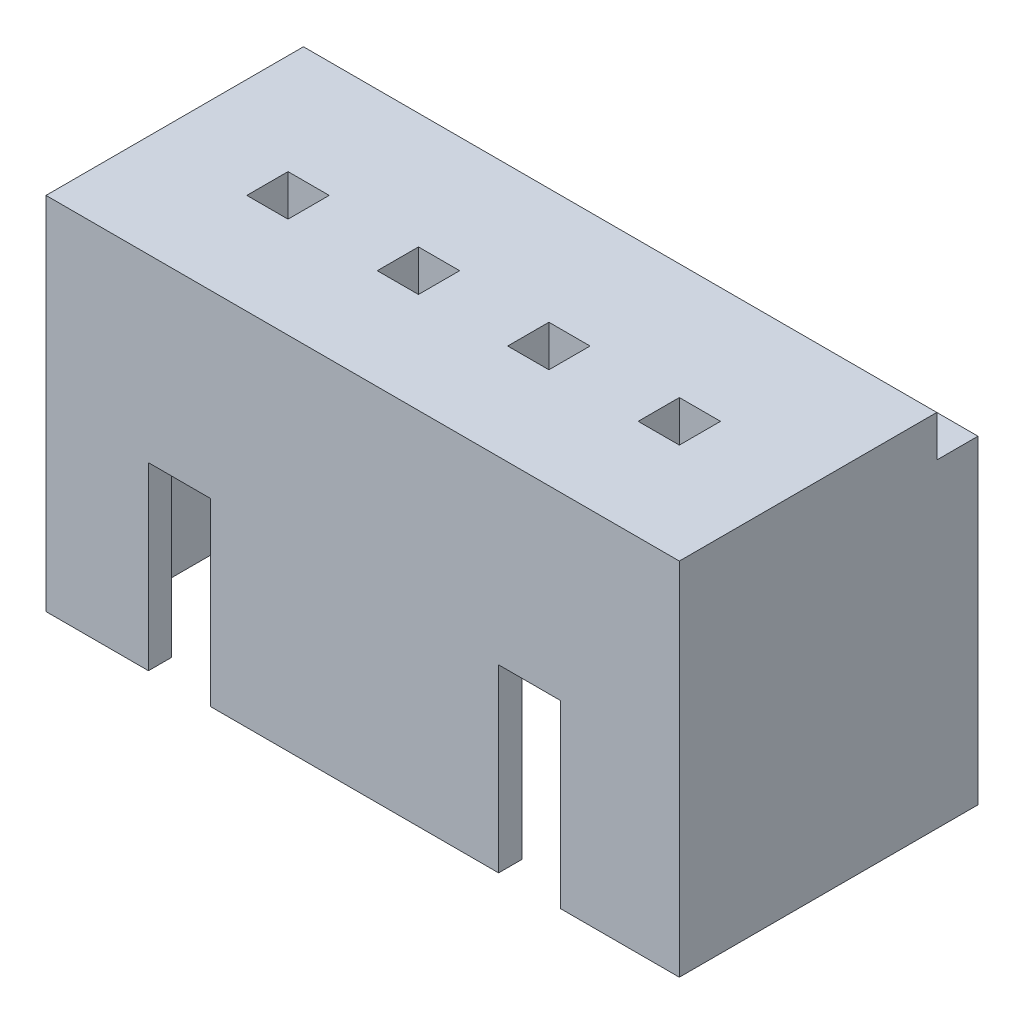
SolidWorks part; units mm, degrees
ref_plane "Front Plane" through (0, 0, 0) normal (0, 0, 1) x (1, 0, 0)
ref_plane "Top Plane" through (0, 0, 0) normal (0, 1, 0) x (1, 0, 0)
ref_plane "Right Plane" through (0, 0, 0) normal (1, 0, 0) x (0, 0, -1)
sketch "Sketch1" plane through (0, 0, 0) normal (0, 1, 0) x (1, 0, 0)
  line L1 (-6.15, -2.9) -> (6.15, -2.9)
  line L2 (-6.15, -2.9) -> (-6.15, 2.9)
  line L3 (-6.15, 2.9) -> (6.15, 2.9)
  line L4 (6.15, -2.9) -> (6.15, 2.9)
  line L5 (-6.15, -2.9) -> (6.15, 2.9) construction
  line L6 (-6.15, 2.9) -> (6.15, -2.9) construction
  point P0 (0, 0)
  dimension "D1" = 12.3
  dimension "D2" = 5.8
extrude "Boss-Extrude1" add sketch "Sketch1" along normal blind 7
sketch "Sketch3" plane through (0, 0, 0) normal (0, -1, 0) x (1, 0, 0)
  line L1 (-5.5, -2.45) -> (5.5, -2.45)
  line L2 (-5.5, -2.45) -> (-5.5, 2.45)
  line L3 (-5.5, 2.45) -> (5.5, 2.45)
  line L4 (5.5, -2.45) -> (5.5, 2.45)
  line L5 (-5.5, -2.45) -> (5.5, 2.45) construction
  line L6 (-5.5, 2.45) -> (5.5, -2.45) construction
  point P0 (0, 0)
  dimension "D1" = 11
  dimension "D2" = 4.9
extrude "Cut-Extrude1" cut sketch "Sketch3" against normal blind 5
sketch "Sketch4" plane through (0, 0, 2.9) normal (0, 0, 1) x (1, 0, 0)
  line L0 (-6.15, 0) -> (6.15, 0) construction
  line L1 (-4.16, 0) -> (-2.96, 0)
  line L2 (-4.16, 0) -> (-4.16, 3.5)
  line L3 (-4.16, 3.5) -> (-2.96, 3.5)
  line L4 (-2.96, 0) -> (-2.96, 3.5)
  line L6 (2.64, 0) -> (3.84, 0)
  line L7 (2.64, 0) -> (2.64, 3.5)
  line L8 (2.64, 3.5) -> (3.84, 3.5)
  line L9 (3.84, 0) -> (3.84, 3.5)
  dimension "D1" = 1.2
  dimension "D2" = 1.2
  dimension "D3" = 4.16
  dimension "D4" = 8
  dimension "D5" = 3.5
extrude "Cut-Extrude2" cut sketch "Sketch4" against normal blind 4
sketch "Sketch5" plane through (0, 7, 0) normal (0, 1, 0) x (1, 0, 0)
  line L0 (6.15, -2.9) -> (6.15, 2.9) construction
  line L1 (6.15, 2.1) -> (-6.15, 2.1)
  line L2 (6.15, 2.1) -> (6.15, 2.9)
  line L3 (6.15, 2.9) -> (-6.15, 2.9)
  line L4 (-6.15, 2.1) -> (-6.15, 2.9)
  dimension "D1" = 0.8
extrude "Cut-Extrude3" cut sketch "Sketch5" against normal blind 0.8 contours L1 L4 L3 L2
sketch "Sketch6" plane through (0, 7, 0) normal (0, 1, 0) x (1, 0, 0)
  line L0 (3.4, -0.15) -> (3.4, -0.95) construction
  line L1 (4.2, -0.95) -> (3.4, -0.95)
  line L2 (4.2, -0.95) -> (4.2, -0.15)
  line L3 (4.2, -0.15) -> (3.4, -0.15)
  line L4 (3.4, -0.95) -> (3.4, -0.15)
  line L5 (-0.8667, -0.15) -> (-1.6667, -0.15) construction
  line L6 (-0.8667, -0.95) -> (-1.6667, -0.95)
  line L7 (-0.8667, -0.95) -> (-0.8667, -0.15)
  line L8 (-0.8667, -0.15) -> (-1.6667, -0.15)
  line L9 (-1.6667, -0.95) -> (-1.6667, -0.15)
  line L10 (-1.6667, 0.45) -> (-1.6667, -0.95) construction
  line L11 (-4.2, -0.15) -> (-4.2, -0.95) construction
  line L12 (1.6667, -0.95) -> (0.8667, -0.95)
  line L13 (1.6667, -0.95) -> (1.6667, -0.15)
  line L14 (1.6667, -0.15) -> (0.8667, -0.15)
  line L15 (0.8667, -0.95) -> (0.8667, -0.15)
  line L16 (-3.4, -0.95) -> (-4.2, -0.95)
  line L17 (-3.4, -0.95) -> (-3.4, -0.15)
  line L18 (-3.4, -0.15) -> (-4.2, -0.15)
  line L19 (-4.2, -0.95) -> (-4.2, -0.15)
extrude "Cut-Extrude4" cut sketch "Sketch6" against normal blind 10
sketch "Sketch7" plane through (0, 5, 0) normal (0, -1, 0) x (1, 0, 0)
  line L0 (5.5, -2.45) -> (5.5, 2.45) construction
  line L1 (-5.5, -2.45) -> (5.5, -2.45)
  line L2 (-5.5, -2.45) -> (-5.5, -1.45)
  line L3 (-5.5, -1.45) -> (5.5, -1.45)
  line L4 (5.5, -2.45) -> (5.5, -1.45)
  dimension "D1" = 1
extrude "Cut-Extrude5" cut sketch "Sketch7" against normal blind 0.3
